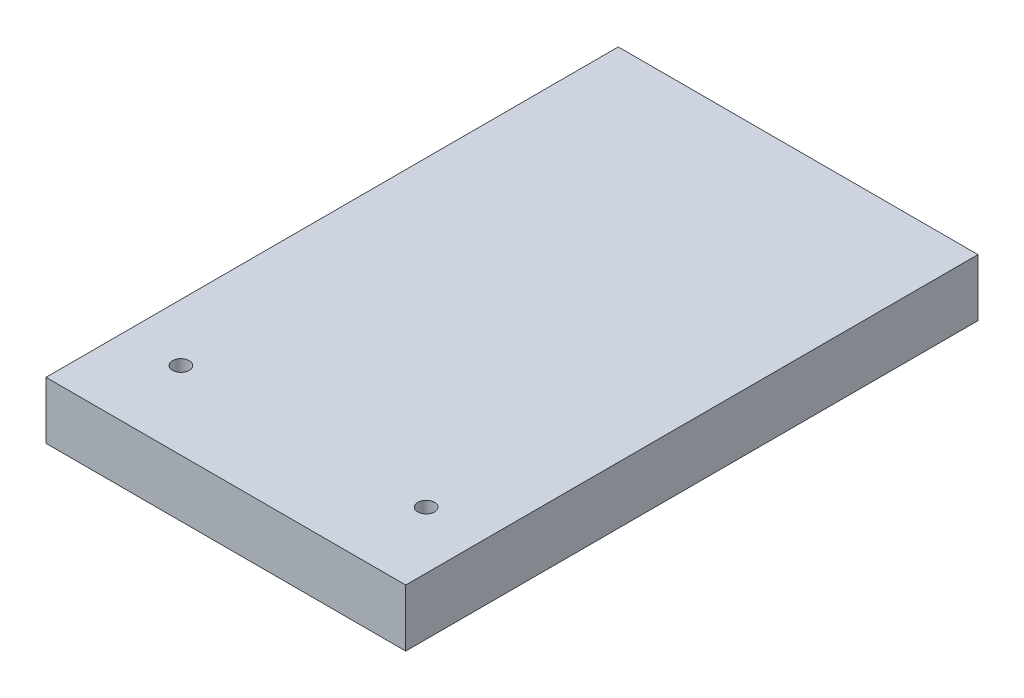
SolidWorks part; units mm, degrees
ref_plane "Front Plane" through (0, 0, 0) normal (0, 0, 1) x (1, 0, 0)
ref_plane "Top Plane" through (0, 0, 0) normal (0, 1, 0) x (1, 0, 0)
ref_plane "Right Plane" through (0, 0, 0) normal (1, 0, 0) x (0, 0, -1)
sketch "Sketch1" plane through (0, 0, 0) normal (0, 1, 0) x (1, 0, 0)
  line L1 (-44, 70) -> (44, 70)
  line L2 (-44, 70) -> (-44, -70)
  line L3 (-44, -70) -> (44, -70)
  line L4 (44, 70) -> (44, -70)
  dimension "D1" = 140
  dimension "D2" = 88
  dimension "D3" = 44
  dimension "D4" = 70
extrude "Boss-Extrude1" add sketch "Sketch1" along normal blind 14
sketch "Sketch2" plane through (0, 14, 0) normal (0, 1, 0) x (1, 0, 0)
  line L0 (44, -70) -> (44, 70) construction
  line L2 (-44, -70) -> (44, -70) construction
  circle A0 centre (-30, -51) radius 2.05
  circle A1 centre (30, -51) radius 2.05
  point P4 (0, 0)
  dimension "D1" = 4.1
  dimension "D2" = 4.1
  dimension "D3" = 60
  dimension "D4" = 14
  dimension "D5" = 19
  dimension "D6" = 19
extrude "Cut-Extrude1" cut sketch "Sketch2" against normal blind 14
